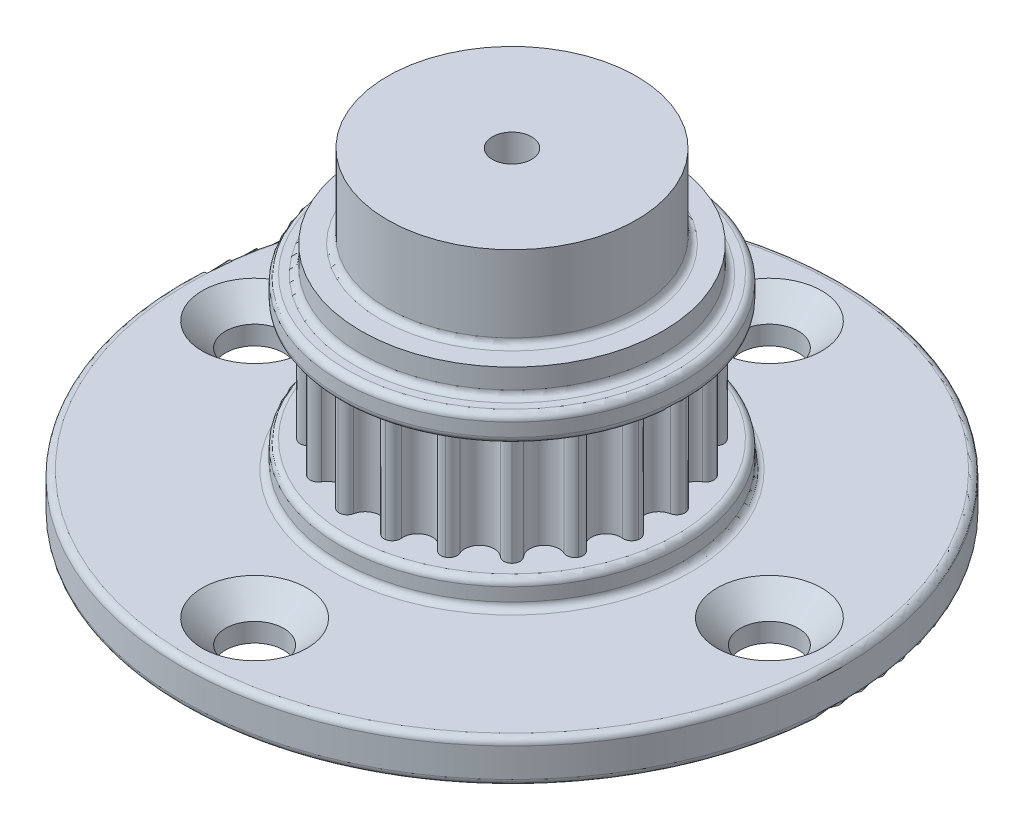
SolidWorks part; units mm, degrees
ref_plane "Front Plane" through (0, 0, 0) normal (0, 0, 1) x (1, 0, 0)
ref_plane "Top Plane" through (0, 0, 0) normal (0, 1, 0) x (1, 0, 0)
ref_plane "Right Plane" through (0, 0, 0) normal (1, 0, 0) x (0, 0, -1)
ref_plane "Plane1" through (0, 0, 0) normal (-0.7071, 0, 0.7071) x (0.7071, 0, 0.7071)
sketch "Sketch1" plane through (0, 0, 0) normal (0, 1, 0) x (1, 0, 0)
  line L0 (0, 0) -> (0, 9.1676) construction
  line L1 (0, 0) -> (2.731, 8.405) construction
  circle A0 centre (0, 0) radius 9.1676 construction
  circle A1 centre (0, 0) radius 7.9476 construction
  circle A2 centre (0, 8.8376) radius 0.89 construction
  circle A5 centre (2.731, 8.405) radius 0.89 construction
  arc A6 (0, 7.9476) -> (0.8721, 8.6598) centre (0, 8.8376) ccw
  arc A7 (0.8721, 8.6598) -> (1.4405, 9.0537) centre (1.362, 8.5599) cw
  arc A8 (1.4277, 9.0557) -> (1.8466, 8.5054) centre (1.3498, 8.5618) cw
  arc A9 (2.4559, 7.5586) -> (1.8466, 8.5054) centre (2.731, 8.405) cw
  arc A10 (1.4405, 9.0537) -> (1.4277, 9.0557) centre (0, 0) cw
  arc A11 (0, 7.9476) -> (2.4559, 7.5586) centre (0, 0) ccw
  dimension "D1" = 18.3352
  dimension "D3" = 1.78
  dimension "D4" = 0.5
  dimension "D2" = 1.22
  dimension "D5" = 18
extrude "Boss-Extrude1" add sketch "Sketch1" along normal mid plane 7.112 contours A6 A11 A9 A8 A7
ref_axis "Axis1" through (0, 3.3, 0) along (0, -1, 0)
pattern_circular "CirPattern1" count 20 over 360 about axis through (0, 0, 0) along (0, 1, 0) of "Boss-Extrude1"
sketch "Sketch2" plane through (0, 0, 0) normal (1, 0, 0) x (0, 0, -1)
  line L10 (0, 3.5) -> (10.3423, 3.5) construction
  line L11 (0, 3.5) -> (0, 5.0875) construction
  line L12 (0, 5.0875) -> (10.3423, 5.0875)
  line L15 (10.3423, 3.5) -> (10.3423, 5.0875) construction
  line L20 (0, 3.3) -> (0, -3.3) construction
  line L22 (10.3423, 5.0875) -> (0, 5.0875) construction
  line L23 (10.3423, 5.0875) -> (10.3423, 3.5)
  line L24 (10.3423, 3.5) -> (0, 3.5)
  line L25 (0, 5.0875) -> (0, 3.5)
  dimension "D1" = 1.5875
  dimension "D2" = 10.3423
  dimension "D3" = 3.5
revolve "Revolve3" add sketch "Sketch2" angle 360 about axis through (0, 3.3, 0) along (0, -1, 0)
mirror "Mirror1" about plane through (0, 0, 0) normal (0, 1, 0) of "Revolve3"
sketch "Sketch9" plane through (0, -5.0875, 0) normal (0, -1, 0) x (1, 0, 0)
  circle A0 centre (0, 0) radius 19.8438
  circle A1 centre (0, 0) radius 1.5
  dimension "D1" = 3
  dimension "D2" = 39.6875
extrude "Boss-Extrude2" add sketch "Sketch9" along normal blind 2.54
sketch "Sketch3" plane through (0, 0, 0) normal (0, 1, 0) x (1, 0, 0)
  circle A0 centre (-15.5, 0) radius 1.7462
  circle A3 centre (0, 15.5) radius 1.7462
  circle A4 centre (15.5, 0) radius 1.7463
  circle A5 centre (0, -15.5) radius 1.7462
  dimension "D3" = 3.4925
  dimension "D1" = 15.5
  dimension "D4" = 4
extrude "Cut-Extrude1" cut sketch "Sketch3" against normal through all both and the other way through all
ref_axis "Axis2" through (-15.5, -7.6275, 0) along (0, 1, 0)
sketch "Sketch6" plane through (0, 0, 0) normal (0, 0, 1) x (1, 0, 0)
  line L0 (-19.1322, -3.5) -> (-11.8678, -3.5) construction
  line L1 (-5.7956, -3.5) -> (-6.4824, -3.5) construction
  line L2 (-11.8678, -3.5) -> (-15.5, -7.1322)
  line L3 (-15.5, -7.1322) -> (-19.1322, -3.5) construction
  line L4 (-18.548, -4.0842) -> (-12.452, -4.0842) construction
  line L5 (-17.2462, -3.998) -> (-13.7538, -3.998) construction
  line L8 (-15.5, -7.1322) -> (-15.5, -3.5)
  line L9 (-15.5, -3.5) -> (-11.8678, -3.5)
  line L10 (-15.5, -7.6275) -> (-15.5, -5.0875) construction
  line L12 (-17.2462, -5.0875) -> (-17.2462, -7.6275) construction
  line L13 (-13.7538, -7.6275) -> (-13.7538, -5.0875) construction
  point P2 (-15.5, -3.998)
  dimension "D1" = 6.096
  dimension "D2" = 0.5842
revolve "Cut-Revolve2" cut sketch "Sketch6" angle 360 about axis through (-15.5, -7.6275, 0) along (0, 1, 0)
hole_wizard "CSK for M3 Flat Head Machine Screw1" positions "3DSketch1" profile "Sketch13" countersink size "M3" standard "ANSI Metric"
sketch3d "3DSketch1"
  line L0 (-15.5, -5.0875, 0) -> (-15.5, -5.3859, 0) construction
  point P0 (-15.5, -5.0875, 0)
sketch "Sketch13" plane through (-15.5, -5.0875, 0) normal (1, 0, 0) x (0, 0, 1)
  line L0 (0, 0) -> (0, 25.9135)
  line L1 (0, 25.9135) -> (1.7, 24.892)
  line L2 (1.7, 24.892) -> (1.7, 1.45)
  line L3 (1.7, 1.45) -> (3.15, 0)
  line L5 (3.15, 0) -> (0, 0)
  line L6 (-1.7, 1.45) -> (-3.15, 0) construction
  line L10 (0, 25.9135) -> (-1.7, 24.892) construction
  line L11 (0, -6.35) -> (0, 107.95) construction
  dimension "Hole Dia." = 3.4
  dimension "Hole Depth" = 24.892
  dimension "Near C'Sink Dia." = 6.3
  dimension "Near C'Sink Angle" = 90
  dimension "Drill Angle" = 118
pattern_circular "CirPattern2" count 4 over 360 about axis through (0, 0, 0) along (0, 1, 0) of "Cut-Revolve2", "CSK for M3 Flat Head Machine Screw1"
sketch "Sketch11" plane through (0, -5.0875, 0) normal (0, -1, 0) x (1, 0, 0)
  circle A0 centre (0, 0) radius 1.5
  dimension "D1" = 3
extrude "Cut-Extrude2" cut sketch "Sketch11" against normal blind 6
sketch "Sketch10" plane through (0, 0, 0) normal (1, 0, 0) x (0, 0, -1)
  line L1 (1.1822, 6.675) -> (7.5, 6.675) construction
  line L2 (1.1822, 6.675) -> (1.1822, 11.675)
  line L3 (1.1822, 11.675) -> (7.5, 11.675)
  line L4 (7.5, 6.675) -> (7.5, 11.675)
  line L5 (0, 0) -> (0, 11.675) construction
  line L6 (10.3423, 5.0875) -> (-10.3423, 5.0875) construction
  line L7 (1.1822, 6.675) -> (9.0875, 6.675) construction
  line L8 (1.1822, 6.675) -> (1.1822, 5.0875)
  line L9 (1.1822, 5.0875) -> (9.0875, 5.0875)
  line L10 (9.0875, 6.675) -> (9.0875, 5.0875)
  line L11 (7.5, 6.675) -> (9.0875, 6.675)
  line L12 (0, 11.675) -> (1.1822, 11.675) construction
  dimension "D1" = 2.3644
  dimension "D2" = 5
  dimension "D3" = 1.5875
  dimension "D4" = 1.5875
  dimension "D5" = 15
revolve "Revolve4" add sketch "Sketch10" angle 360 about L5
fillet "Fillet1" radius 0.3969 8 edges at (0, 5.0875, 10.3423) (0, 3.5, 10.3423) (0, -7.6275, -19.8438) (0, -5.0875, -19.8438) (0, 6.675, -7.5) (0, 5.0875, -9.0875) (0, -3.5, 10.3423) (0, -5.0875, 10.3423)
equation "\"TEETH_NUM\"= 20"
equation "\"TOOTH_PITCH\"= 3mm"
equation "\"PITCH_LINE_OFFSET\"= .015in"
equation "\"DIAMETER_PER_GROOVE\"= \"OUTSIDE_DIAMETER\" / \"TEETH_NUM\" * 1in"
equation "\"PITCH_DIAMETER\"= ( ( \"TEETH_NUM\" * 3 - 1.31 ) / 3.1415 + .415 ) * 1mm"
equation "\"OUTSIDE_DIAMETER\"= \"PITCH_DIAMETER\" - \"PITCH_LINE_OFFSET\" * 2"
equation "\"D1@Sketch1\"=\"OUTSIDE_DIAMETER\""
equation "\"TOOTH_HEIGHT\"= 1.22mm"
equation "\"D2@Sketch1\"=\"TOOTH_HEIGHT\""
equation "\"TOOTH_DIAMETER\"= 1.78mm"
equation "\"INTERNAL_RADIUS\"= .5mm"
equation "\"D3@Sketch1\"=\"TOOTH_DIAMETER\""
equation "\"D5@Sketch1\"=360 / \"TEETH_NUM\""
equation "\"D4@Sketch1\"=\"INTERNAL_RADIUS\""
equation "\"D1@CirPattern1\"=\"TEETH_NUM\""
equation "\"BELT_GAP\"= 7mm"
equation "\"D2@Sketch2\"=\"PITCH_DIAMETER\"/2+1/32"
equation "\"D3@Sketch2\"=\"BELT_GAP\"/2"
